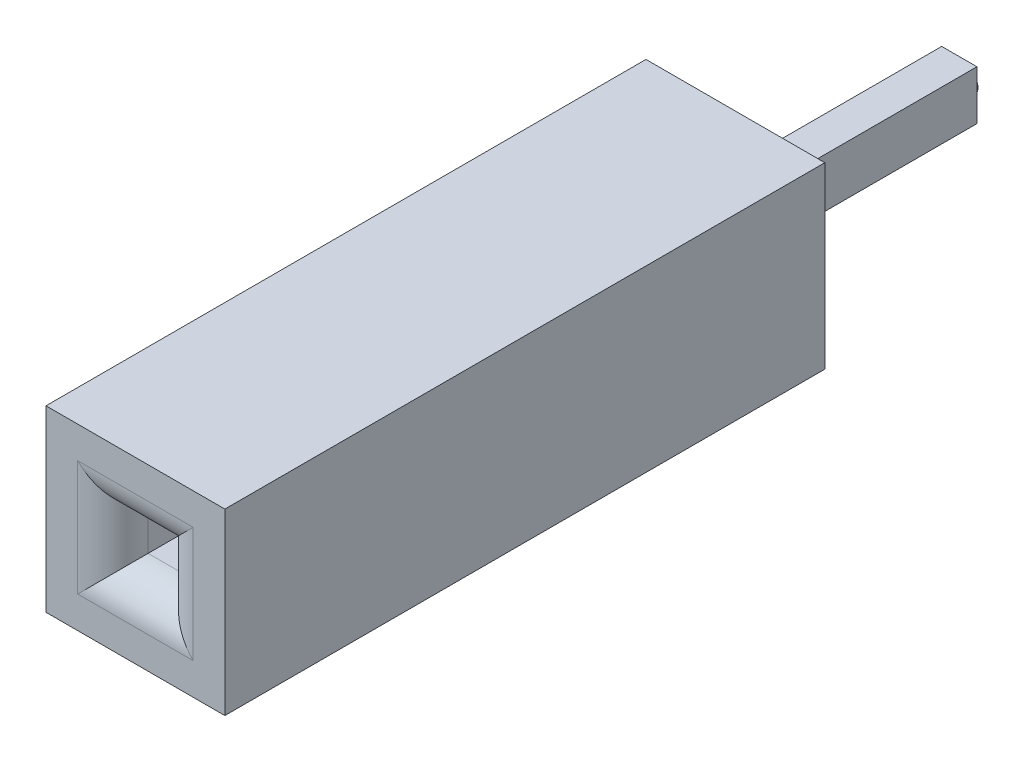
SolidWorks part; units mm, degrees
ref_plane "Front Plane" through (0, 0, 0) normal (0, 0, 1) x (1, 0, 0)
ref_plane "Top Plane" through (0, 0, 0) normal (0, 1, 0) x (1, 0, 0)
ref_plane "Right Plane" through (0, 0, 0) normal (1, 0, 0) x (0, 0, -1)
sketch "Sketch1" plane through (0, 0, 0) normal (0, 0, 1) x (1, 0, 0)
  line L1 (-1.27, -1.27) -> (1.27, -1.27)
  line L2 (-1.27, -1.27) -> (-1.27, 1.27)
  line L3 (-1.27, 1.27) -> (1.27, 1.27)
  line L4 (1.27, -1.27) -> (1.27, 1.27)
  line L5 (-1.27, -1.27) -> (1.27, 1.27) construction
  line L6 (-1.27, 1.27) -> (1.27, -1.27) construction
  point P0 (0, 0)
  dimension "D1" = 2.54
  dimension "D2" = 2.54
extrude "Boss-Extrude1" add sketch "Sketch1" along normal blind 8.52
sketch "Sketch2" plane through (0, 0, 8.52) normal (0, 0, 1) x (1, 0, 0)
  line L1 (-0.32, -0.32) -> (0.32, -0.32)
  line L2 (-0.32, -0.32) -> (-0.32, 0.32)
  line L3 (-0.32, 0.32) -> (0.32, 0.32)
  line L4 (0.32, -0.32) -> (0.32, 0.32)
  line L5 (-0.32, -0.32) -> (0.32, 0.32) construction
  line L6 (-0.32, 0.32) -> (0.32, -0.32) construction
  point P0 (0, 0)
  dimension "D1" = 0.64
  dimension "D2" = 0.64
extrude "Cut-Extrude1" cut sketch "Sketch2" against normal blind 6.5
fillet "Fillet1" radius 0.5 4 edges at (0, -0.32, 8.52) (0.32, 0, 8.52) (0, 0.32, 8.52) (-0.32, 0, 8.52)
sketch "Sketch4" plane through (0, 0, 0) normal (0, 0, -1) x (1, 0, 0)
  line L1 (0.25, -0.35) -> (-0.25, -0.35)
  line L2 (0.25, -0.35) -> (0.25, 0.35)
  line L3 (0.25, 0.35) -> (-0.25, 0.35)
  line L4 (-0.25, -0.35) -> (-0.25, 0.35)
  line L5 (0.25, -0.35) -> (-0.25, 0.35) construction
  line L6 (0.25, 0.35) -> (-0.25, -0.35) construction
  point P0 (0, 0)
  dimension "D1" = 0.5
  dimension "D2" = 0.7
extrude "Boss-Extrude2" add sketch "Sketch4" along normal blind 3.18
sketch "Sketch5" plane through (0, 0, 2.02) normal (0, 0, 1) x (1, 0, 0)
  circle A0 centre (0, 0) radius 0.255
  dimension "D1" = 0.51
extrude "Cut-Extrude4" cut sketch "Sketch5" against normal blind 0.26
sketch "Sketch6" plane through (0, 0, -3.18) normal (0, 0, -1) x (-1, 0, 0)
  circle A0 centre (0, 0) radius 0.1654
extrude "Boss-Extrude3" add sketch "Sketch6" along normal blind 0.1
